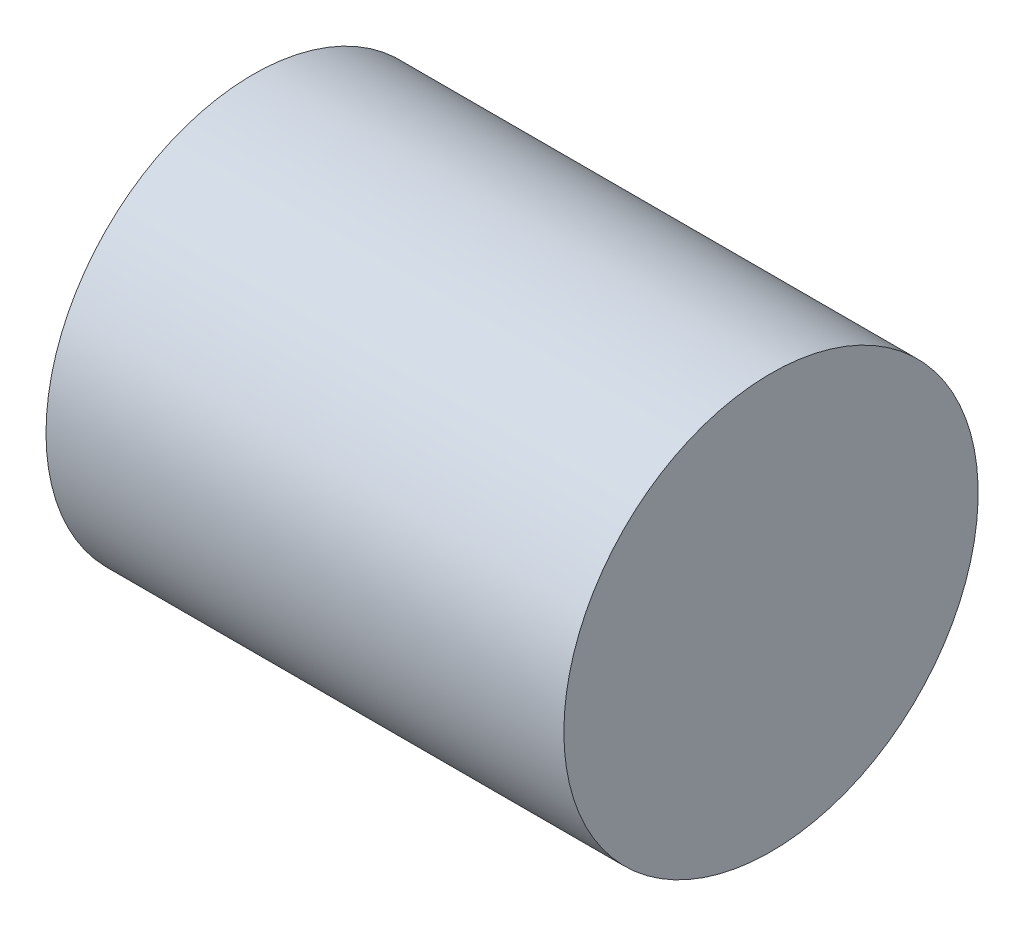
SolidWorks part; units mm, degrees
material "1023 al carbonio, lamiera (SS)"
ref_plane "Piano frontale" through (0, 0, 0) normal (0, 0, 1) x (1, 0, 0)
ref_plane "Piano superiore" through (0, 0, 0) normal (0, 1, 0) x (1, 0, 0)
ref_plane "Piano destro" through (0, 0, 0) normal (1, 0, 0) x (0, 0, -1)
sketch "Schizzo1" plane through (0, 0, 0) normal (0, 0, 1) x (1, 0, 0)
  line L1 (0, 0) -> (40, 0)
  line L2 (0, 0) -> (0, 16)
  line L3 (0, 16) -> (40, 16)
  line L4 (40, 0) -> (40, 16)
  dimension "D1" = 16
  dimension "D2" = 40
revolve "Rivoluzione1" add sketch "Schizzo1" angle 360 about L3
